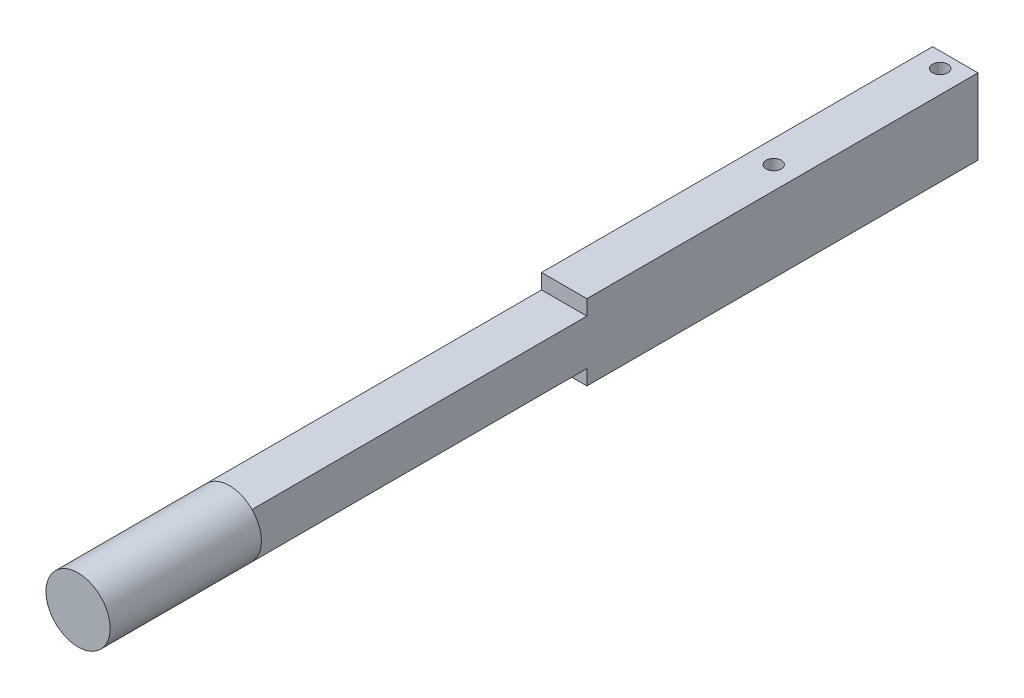
SolidWorks part; units mm, degrees
ref_plane "Front Plane" through (0, 0, 0) normal (0, 0, 1) x (1, 0, 0)
ref_plane "Top Plane" through (0, 0, 0) normal (0, 1, 0) x (1, 0, 0)
ref_plane "Right Plane" through (0, 0, 0) normal (1, 0, 0) x (0, 0, -1)
sketch "Sketch2" plane through (0, 0, 0) normal (0, 0, 1) x (1, 0, 0)
  line L1 (-19.05, 19.05) -> (19.05, 19.05)
  line L2 (-19.05, 19.05) -> (-19.05, -19.05)
  line L3 (-19.05, -19.05) -> (19.05, -19.05)
  line L4 (19.05, 19.05) -> (19.05, -19.05)
  line L5 (-19.05, 19.05) -> (19.05, -19.05) construction
  line L6 (-19.05, -19.05) -> (19.05, 19.05) construction
  point P0 (0, 0)
  dimension "D1" = 38.1
  dimension "D2" = 38.1
extrude "Boss-Extrude1" add sketch "Sketch2" along normal blind 609.6
sketch "Sketch3" plane through (0, 0, 609.6) normal (0, 0, 1) x (1, 0, 0)
  circle A0 centre (0, 0) radius 26.9408
extrude "Boss-Extrude2" add sketch "Sketch3" along normal blind 127
sketch "Sketch4" plane through (0, -19.05, 0) normal (0, -1, 0) x (1, 0, 0)
  line L0 (19.05, 0) -> (19.05, 152.4)
  line L1 (19.05, 609.6) -> (19.05, 0) construction
  line L2 (19.05, 152.4) -> (-19.05, 152.4)
  line L3 (-19.05, 609.6) -> (-19.05, 0) construction
  circle A0 centre (0, 152.4) radius 6.35
  dimension "D2" = 12.7
  dimension "D1" = 152.4
extrude "Cut-Extrude2" cut sketch "Sketch4" against normal blind 127 contours L2 A0 | L2 A0
sketch "Sketch5" plane through (19.05, 0, 0) normal (1, 0, 0) x (0, 0, -1)
  line L0 (0, 0) -> (0, 31.75)
  line L1 (0, 31.75) -> (-328.3833, 31.75)
  line L3 (0, -31.75) -> (-328.3833, -31.75)
  line L4 (-328.3833, 31.75) -> (-328.3833, -31.75)
  line L5 (0, 0) -> (-328.3833, -31.75) construction
  line L6 (0, 0) -> (-328.3833, 31.75) construction
  line L7 (0, 0) -> (0, -31.75)
  point P0 (0, 0)
  dimension "D1" = 63.5
extrude "Boss-Extrude3" add sketch "Sketch5" against normal blind 38.1
sketch "Sketch6" plane through (0, -31.75, 0) normal (0, -1, 0) x (1, 0, 0)
  line L0 (0, 0) -> (0, 152.4942)
  circle A0 centre (0, 152.4942) radius 6.35
  dimension "D1" = 12.7
extrude "Cut-Extrude4" cut sketch "Sketch6" against normal through all
sketch "Sketch7" plane through (0, -31.75, 0) normal (0, -1, 0) x (1, 0, 0)
  line L0 (0, 0) -> (0, 12.7)
  circle A0 centre (0, 12.7) radius 6.35
  dimension "D2" = 12.7
  dimension "D1" = 12.7
extrude "Cut-Extrude5" cut sketch "Sketch7" against normal blind 533.4
